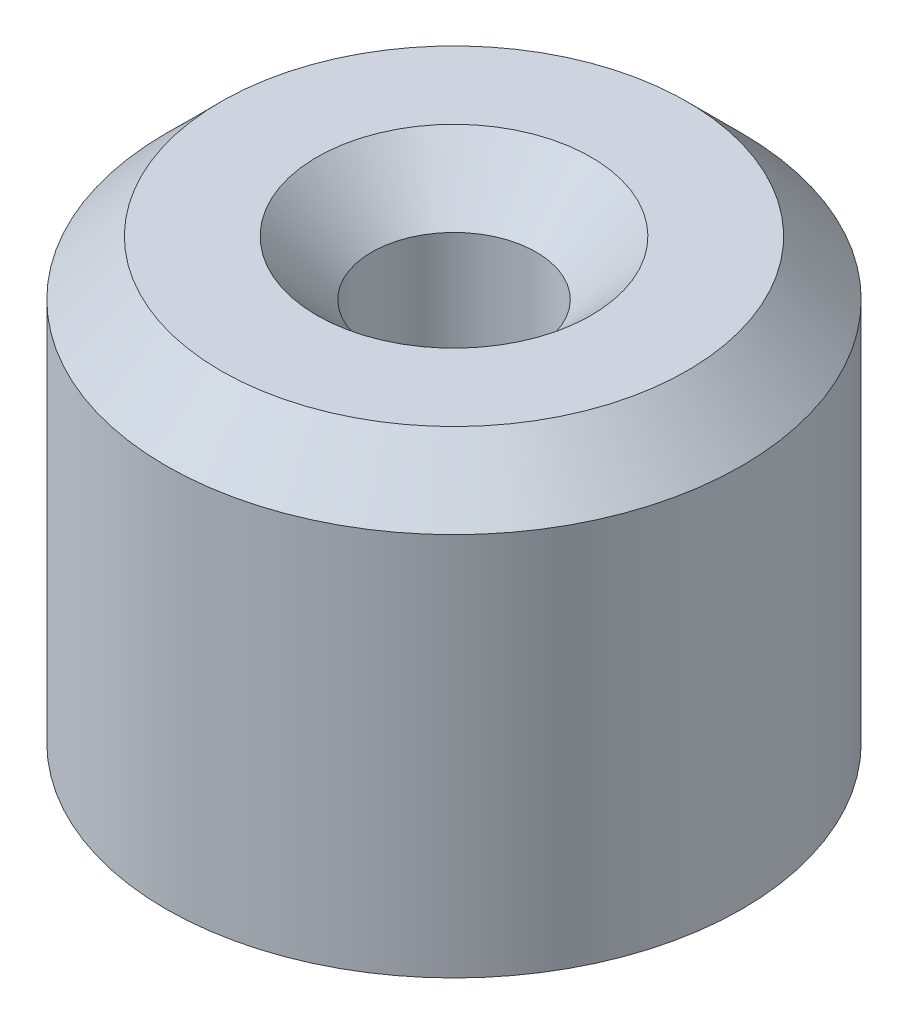
SolidWorks part; units mm, degrees
ref_plane "Front Plane" through (0, 0, 0) normal (0, 0, 1) x (1, 0, 0)
ref_plane "Top Plane" through (0, 0, 0) normal (0, 1, 0) x (1, 0, 0)
ref_plane "Right Plane" through (0, 0, 0) normal (1, 0, 0) x (0, 0, -1)
sketch "Sketch1" plane through (0, 0, 0) normal (0, 1, 0) x (1, 0, 0)
  circle A0 centre (0, 0) radius 5.25
  dimension "D1" = 10.5
extrude "Boss-Extrude1" add sketch "Sketch1" along normal blind 8
sketch "Sketch2" plane through (0, 8, 0) normal (0, 1, 0) x (1, 0, 0)
  circle A0 centre (0, 0) radius 1.5
  dimension "D1" = 3
extrude "Cut-Extrude1" cut sketch "Sketch2" against normal offset from surface (6 mm away) 2 up to face at (0, 0, 5.25)
shell "Shell1" thickness 1.1
sketch "Sketch3" plane through (0, 2, 0) normal (0, 1, 0) x (1, 0, 0)
  circle A0 centre (0, 0) radius 1.5
extrude "Cut-Extrude2" cut sketch "Sketch3" against normal through all
chamfer "Chamfer1" distance 1 angle 45 1 edges at (0, 8, 5.25)
chamfer "Chamfer2" distance 1 angle 45 1 edges at (0, 8, 1.5)
